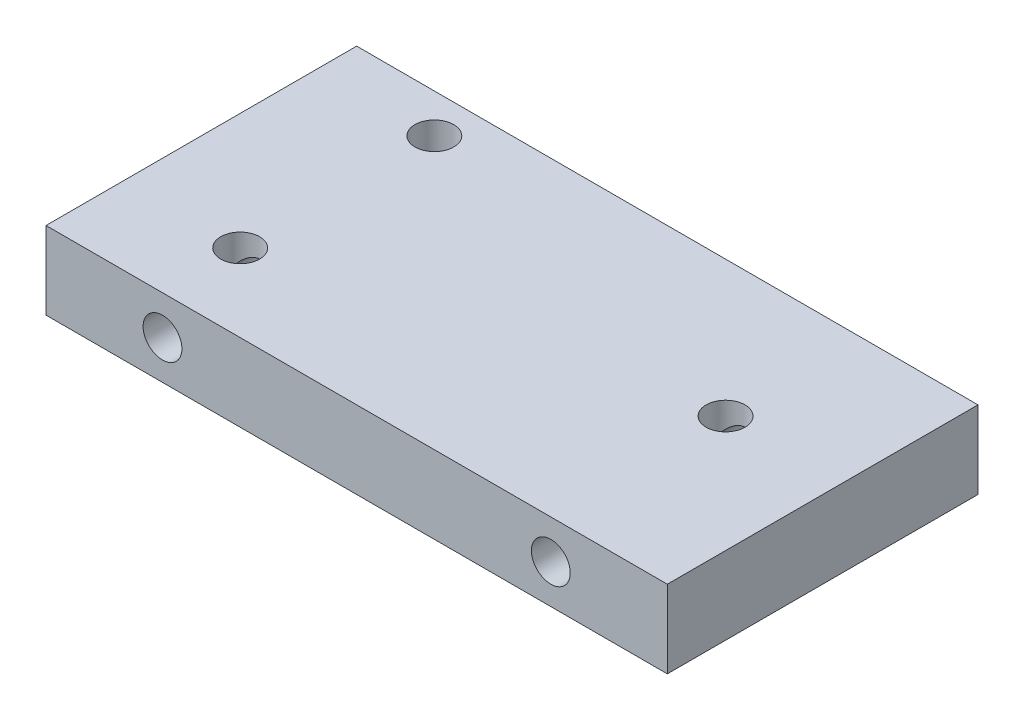
SolidWorks part; units mm, degrees
ref_plane "Front Plane" through (0, 0, 0) normal (0, 0, 1) x (1, 0, 0)
ref_plane "Top Plane" through (0, 0, 0) normal (0, 1, 0) x (1, 0, 0)
ref_plane "Right Plane" through (0, 0, 0) normal (1, 0, 0) x (0, 0, -1)
sketch "Sketch1" plane through (0, 0, 0) normal (0, 1, 0) x (1, 0, 0)
  line L1 (-82.9523, 61.5815) -> (117.0477, 61.5815)
  line L2 (-82.9523, 61.5815) -> (-82.9523, -38.4185)
  line L3 (-82.9523, -38.4185) -> (117.0477, -38.4185)
  line L4 (117.0477, 61.5815) -> (117.0477, -38.4185)
  dimension "D1" = 200
  dimension "D2" = 100
extrude "Boss-Extrude1" add sketch "Sketch1" along normal blind 25
sketch "Sketch2" plane through (0, 0, 38.4185) normal (0, 0, 1) x (1, 0, 0)
  line L0 (-82.9523, 12.5) -> (117.0477, 12.5) construction
  line L1 (-82.9523, 25) -> (-82.9523, 0) construction
  line L2 (117.0477, 25) -> (117.0477, 0) construction
  line L3 (-45.4523, 25) -> (-45.4523, 0) construction
  line L4 (-82.9523, 25) -> (117.0477, 25) construction
  line L5 (-82.9523, 0) -> (117.0477, 0) construction
  line L6 (79.5477, 25) -> (79.5477, 0) construction
  circle A0 centre (-45.4523, 12.5) radius 6.25
  circle A1 centre (79.5477, 12.5) radius 6.25
  dimension "D3" = 12.5
  dimension "D4" = 12.5
  dimension "D1" = 37.5
  dimension "D2" = 37.5
extrude "Cut-Extrude1" cut sketch "Sketch2" against normal blind 87.5 contours A0 | A1
sketch "Sketch3" plane through (0, 25, 0) normal (0, 1, 0) x (1, 0, 0)
  line L0 (-45.4523, -38.4185) -> (-45.4523, 61.5815) construction
  line L1 (-82.9523, -38.4185) -> (117.0477, -38.4185) construction
  line L2 (117.0477, 61.5815) -> (-82.9523, 61.5815) construction
  line L3 (79.5477, 61.5815) -> (79.5477, -38.4185) construction
  line L4 (-82.9523, 61.5815) -> (-82.9523, -38.4185) construction
  line L5 (117.0477, -38.4185) -> (117.0477, 61.5815) construction
  line L6 (-45.4523, 49.0815) -> (-45.4523, -13.4185)
  line L7 (-45.4523, 17.8315) -> (117.0477, 17.8315) construction
  circle A0 centre (-45.4523, -13.4185) radius 6.25
  circle A1 centre (-45.4523, 49.0815) radius 6.25
  circle A2 centre (79.5477, 17.8315) radius 6.25
  dimension "D3" = 12.5
  dimension "D4" = 12.5
  dimension "D7" = 12.5
  dimension "D1" = 37.5
  dimension "D2" = 37.5
  dimension "D5" = 12.5
  dimension "D6" = 25
extrude "Cut-Extrude2" cut sketch "Sketch3" against normal blind 18.75
